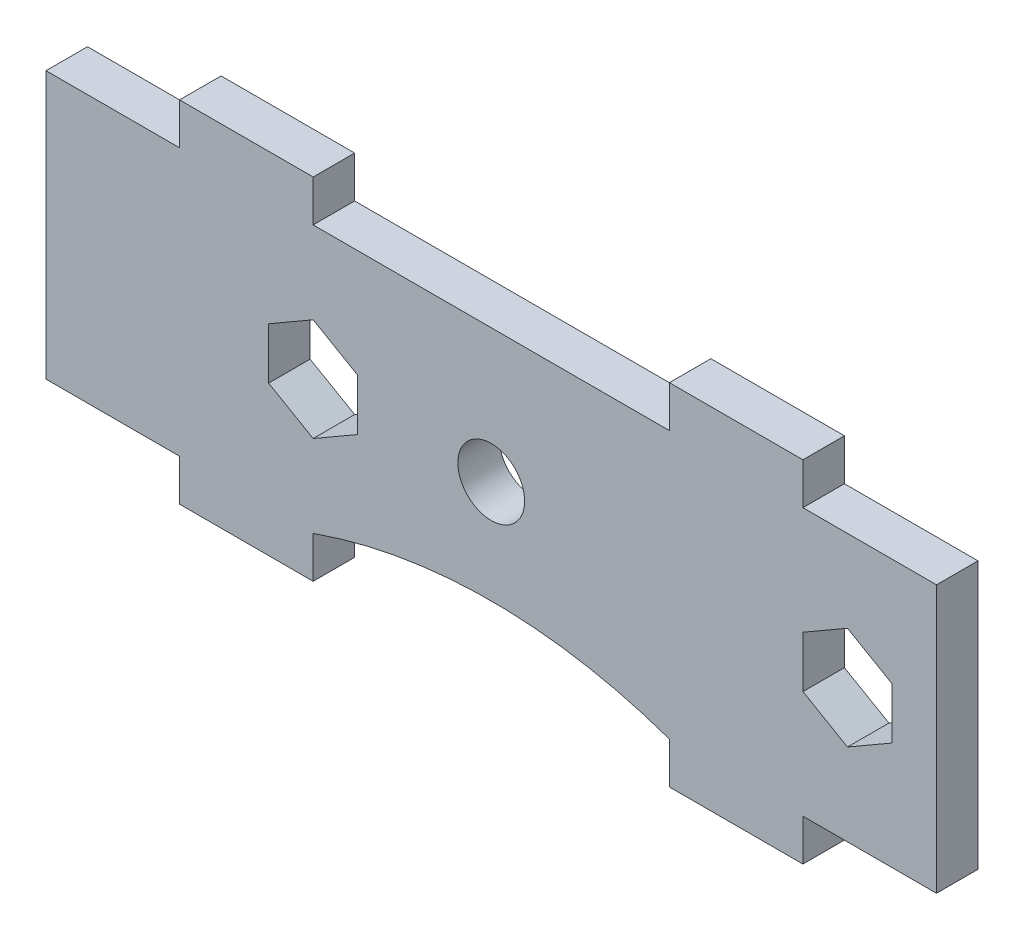
SolidWorks part; units mm, degrees
ref_plane "Front Plane" through (0, 0, 0) normal (0, 0, 1) x (1, 0, 0)
ref_plane "Top Plane" through (0, 0, 0) normal (0, 1, 0) x (1, 0, 0)
ref_plane "Right Plane" through (0, 0, 0) normal (1, 0, 0) x (0, 0, -1)
sketch "Sketch1" plane through (0, 0, 0) normal (0, 0, 1) x (1, 0, 0)
  line L0 (0, 17.2471) -> (0, -17.2471) construction
  line L1 (-31.75, 0) -> (31.75, 0) construction
  line L2 (-12.7, 9.525) -> (12.7, 9.525)
  line L3 (-31.75, -9.525) -> (-22.225, -9.525)
  line L4 (-31.75, -9.525) -> (-31.75, 9.525)
  line L5 (-31.75, 9.525) -> (-22.225, 9.525)
  line L6 (31.75, -9.525) -> (31.75, 9.525)
  line L7 (-31.75, -9.525) -> (31.75, 9.525) construction
  line L8 (-31.75, 9.525) -> (31.75, -9.525) construction
  line L9 (-12.7, -9.525) -> (-12.7, -12.4841)
  line L10 (-22.225, 9.525) -> (-22.225, 12.4841)
  line L11 (-22.225, 12.4841) -> (-12.7, 12.4841)
  line L12 (-12.7, 9.525) -> (-12.7, 12.4841)
  line L13 (-22.225, -12.4841) -> (-12.7, -12.4841)
  line L14 (-22.225, -9.525) -> (-22.225, -12.4841)
  line L15 (22.225, -9.525) -> (22.225, -12.4841)
  line L16 (22.225, -12.4841) -> (12.7, -12.4841)
  line L17 (12.7, -9.525) -> (12.7, -12.4841)
  line L18 (12.7, 9.525) -> (12.7, 12.4841)
  line L19 (22.225, 12.4841) -> (12.7, 12.4841)
  line L20 (22.225, 9.525) -> (22.225, 12.4841)
  line L21 (22.225, -9.525) -> (31.75, -9.525)
  line L22 (22.225, 9.525) -> (31.75, 9.525)
  line L23 (-12.7, -9.525) -> (12.7, -9.525)
  circle A0 centre (0, 0) radius 2.3812
  dimension "D1" = 4.7625
  dimension "D2" = 19.05
  dimension "D3" = 63.5
  dimension "D4" = 9.525
  dimension "D5" = 2.9591
  dimension "D6" = 25.4
extrude "Boss-Extrude1" add sketch "Sketch1" along normal mid plane 2.9591
sketch "Sketch2" plane through (0, 0, 1.4796) normal (0, 0, 1) x (1, 0, 0)
  line L1 (-12.7, -3.6662) -> (-9.525, -1.8331)
  line L2 (-9.525, -1.8331) -> (-9.525, 1.8331)
  line L3 (-9.525, 1.8331) -> (-12.7, 3.6662)
  line L4 (-12.7, 3.6662) -> (-15.875, 1.8331)
  line L5 (-15.875, 1.8331) -> (-15.875, -1.8331)
  line L6 (-15.875, -1.8331) -> (-12.7, -3.6662)
  circle A0 centre (-12.7, 0) radius 3.175 construction
  dimension "D1" = 6.35
  dimension "D2" = 12.7
extrude "Cut-Extrude1" cut sketch "Sketch2" against normal up to next
sketch "Sketch3" plane through (0, 0, 1.4796) normal (0, 0, 1) x (1, 0, 0)
  line L0 (-9.525, 1.8331) -> (-12.7, 3.6662) construction
  line L1 (25.4, -3.6662) -> (28.575, -1.8331)
  line L2 (28.575, -1.8331) -> (28.575, 1.8331)
  line L3 (28.575, 1.8331) -> (25.4, 3.6662)
  line L4 (25.4, 3.6662) -> (22.225, 1.8331)
  line L5 (22.225, 1.8331) -> (22.225, -1.8331)
  line L6 (22.225, -1.8331) -> (25.4, -3.6662)
  circle A0 centre (25.4, 0) radius 3.175 construction
  dimension "D1" = 25.4
extrude "Cut-Extrude2" cut sketch "Sketch3" against normal up to next
sketch "Sketch4" plane through (0, 0, 1.4796) normal (0, 0, 1) x (1, 0, 0)
  line L0 (-12.7, -9.525) -> (12.7, -9.525)
  arc A0 (-12.7, -9.525) -> (12.7, -9.525) centre (0, -45.446) cw
  dimension "D1" = 38.1
extrude "Cut-Extrude3" cut sketch "Sketch4" against normal through all
